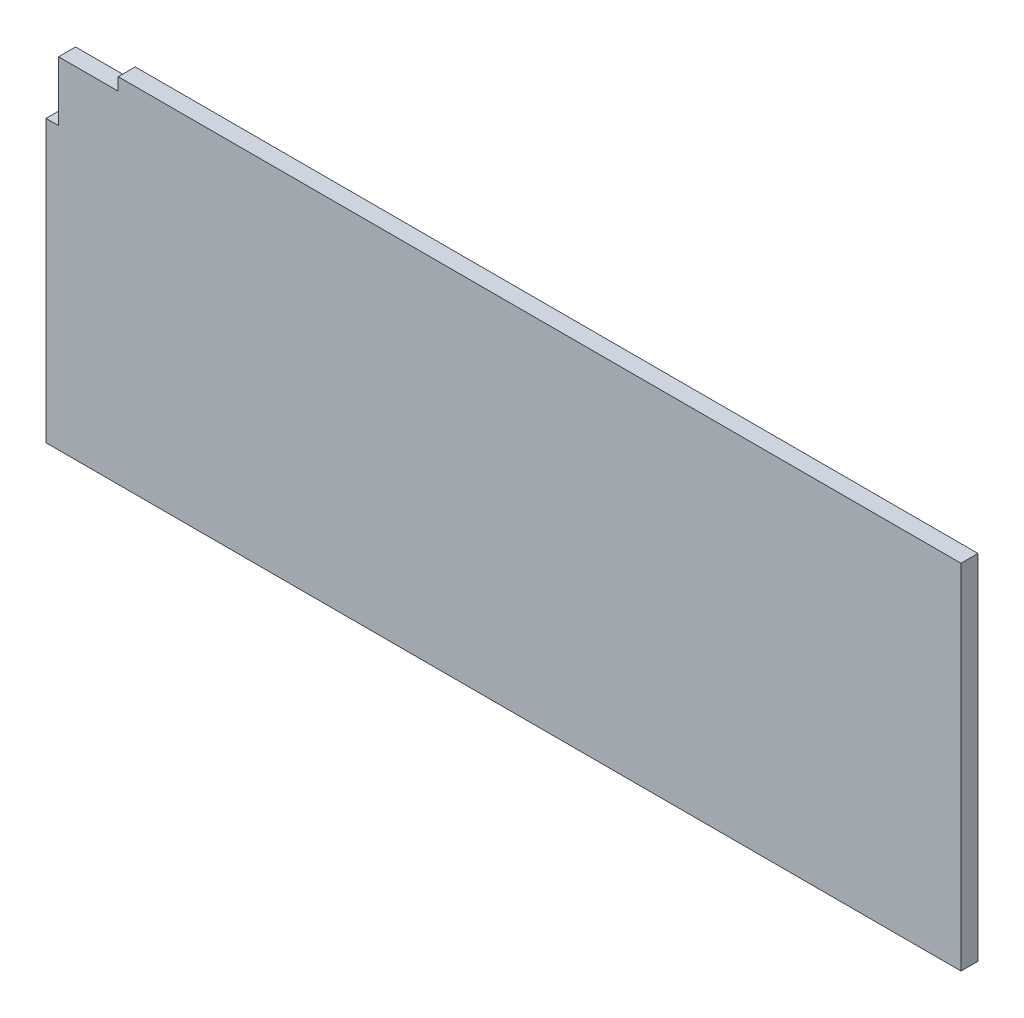
SolidWorks part; units mm, degrees
ref_plane "Front Plane" through (0, 0, 0) normal (0, 0, 1) x (1, 0, 0)
ref_plane "Top Plane" through (0, 0, 0) normal (0, 1, 0) x (1, 0, 0)
ref_plane "Right Plane" through (0, 0, 0) normal (1, 0, 0) x (0, 0, -1)
sketch "Sketch1" plane through (0, 0, 0) normal (0, 0, 1) x (1, 0, 0)
  line L0 (27, 132) -> (27, 127.3)
  line L5 (27, 127.3) -> (4.7, 127.3)
  line L6 (4.7, 127.3) -> (4.7, 105)
  line L7 (4.7, 105) -> (0, 105)
  line L12 (342, 132) -> (342, 0)
  line L13 (342, 0) -> (0, 0)
  line L14 (0, 0) -> (0, 105)
  line L15 (342, 132) -> (27, 132)
  point P2 (0, 0)
  dimension "D1" = 342
  dimension "D2" = 132
  dimension "D7" = 4.7
  dimension "D8" = 4.7
  dimension "D9" = 27
  dimension "D10" = 27
extrude "Boss-Extrude1" add sketch "Sketch1" along normal blind 6.35
